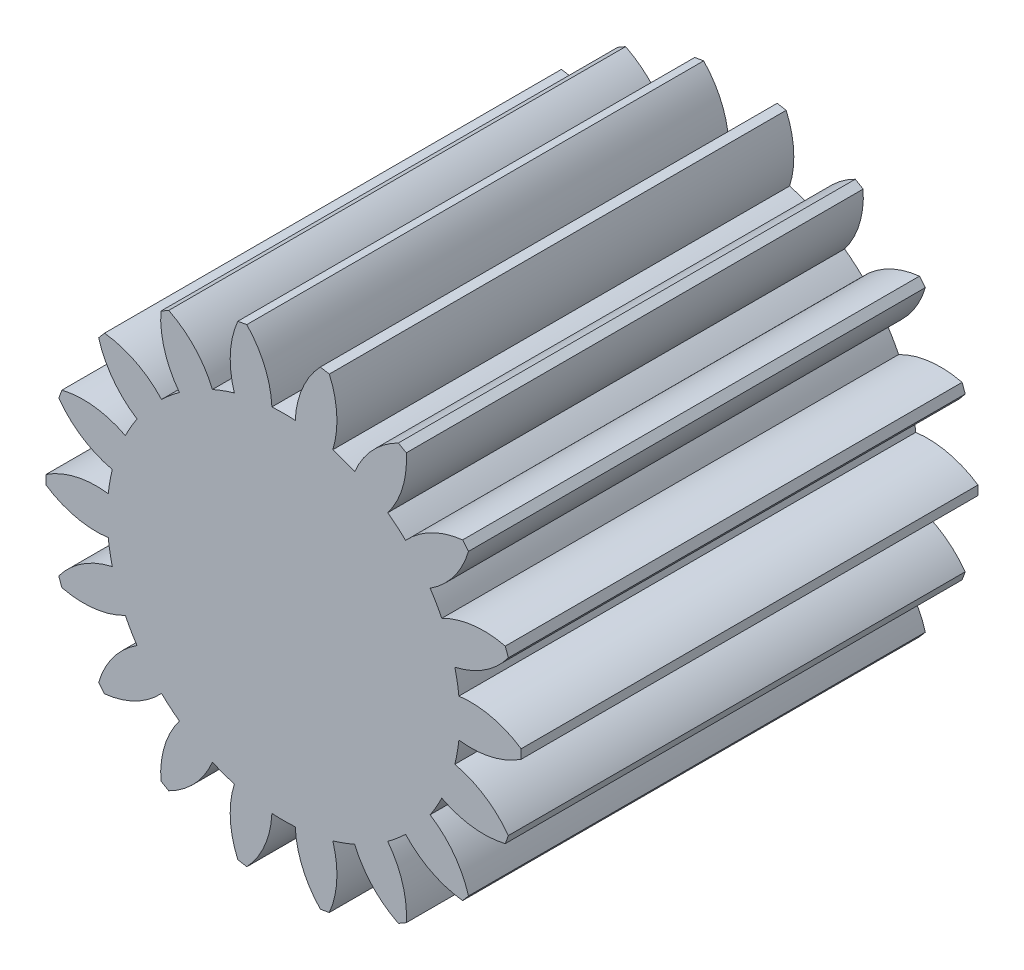
SolidWorks part; units mm, degrees
ref_plane "Front Plane" through (0, 0, 0) normal (0, 0, 1) x (1, 0, 0)
ref_plane "Top Plane" through (0, 0, 0) normal (0, 1, 0) x (1, 0, 0)
ref_plane "Right Plane" through (0, 0, 0) normal (1, 0, 0) x (0, 0, -1)
sketch "Sketch1" plane through (0, 0, 0) normal (0, 0, 1) x (1, 0, 0)
  arc A72 (4.0738, 2.7268) -> (4.9618, 3.9627) centre (2.7672, 4.6025) ccw
  arc A73 (4.9618, 3.9627) -> (4.7641, 4.1983) centre (0, 0) ccw
  arc A74 (4.7641, 4.1983) -> (3.3928, 3.5385) centre (5.0131, 1.9259) ccw
  arc A75 (3.3928, 3.5385) -> (2.8956, 3.9557) centre (0, 0) ccw
  arc A76 (2.8956, 3.9557) -> (3.3073, 5.4207) centre (1.0261, 5.2714) ccw
  arc A77 (3.3073, 5.4207) -> (3.0409, 5.5745) centre (0, 0) ccw
  arc A78 (3.0409, 5.5745) -> (1.9779, 4.4855) centre (4.0521, 3.5244) ccw
  arc A79 (1.9779, 4.4855) -> (1.368, 4.7075) centre (0, 0) ccw
  arc A80 (1.368, 4.7075) -> (1.2538, 6.225) centre (-0.8387, 5.3045) ccw
  arc A81 (1.2538, 6.225) -> (0.9509, 6.2784) centre (0, 0) ccw
  arc A82 (0.9509, 6.2784) -> (0.3245, 4.8914) centre (2.6023, 4.6977) ccw
  arc A83 (0.3245, 4.8914) -> (-0.3245, 4.8914) centre (0, 0) ccw
  arc A84 (-0.3245, 4.8914) -> (-0.9509, 6.2784) centre (-2.6023, 4.6977) ccw
  arc A85 (-0.9509, 6.2784) -> (-1.2538, 6.225) centre (0, 0) ccw
  arc A86 (-1.2538, 6.225) -> (-1.368, 4.7075) centre (0.8387, 5.3045) ccw
  arc A87 (-1.368, 4.7075) -> (-1.9779, 4.4855) centre (0, 0) ccw
  arc A88 (-1.9779, 4.4855) -> (-3.0409, 5.5745) centre (-4.0521, 3.5244) ccw
  arc A89 (-3.0409, 5.5745) -> (-3.3073, 5.4207) centre (0, 0) ccw
  arc A90 (-3.3073, 5.4207) -> (-2.8956, 3.9557) centre (-1.0261, 5.2714) ccw
  arc A91 (-2.8956, 3.9557) -> (-3.3928, 3.5385) centre (0, 0) ccw
  arc A92 (-3.3928, 3.5385) -> (-4.7641, 4.1983) centre (-5.0131, 1.9259) ccw
  arc A93 (-4.7641, 4.1983) -> (-4.9618, 3.9627) centre (0, 0) ccw
  arc A94 (-4.9618, 3.9627) -> (-4.0738, 2.7268) centre (-2.7672, 4.6025) ccw
  arc A95 (-4.0738, 2.7268) -> (-4.3984, 2.1647) centre (0, 0) ccw
  arc A96 (-4.3984, 2.1647) -> (-5.9127, 2.3157) centre (-5.3695, 0.0952) ccw
  arc A97 (-5.9127, 2.3157) -> (-6.0179, 2.0267) centre (0, 0) ccw
  arc A98 (-6.0179, 2.0267) -> (-4.7608, 1.169) centre (-4.1745, 3.3785) ccw
  arc A99 (-4.7608, 1.169) -> (-4.8735, 0.5298) centre (0, 0) ccw
  arc A100 (-4.8735, 0.5298) -> (-6.3481, 0.1538) centre (-5.0782, -1.747) ccw
  arc A101 (-6.3481, 0.1538) -> (-6.3481, -0.1538) centre (0, 0) ccw
  arc A102 (-6.3481, -0.1538) -> (-4.8735, -0.5298) centre (-5.0782, 1.747) ccw
  arc A103 (-4.8735, -0.5298) -> (-4.7608, -1.169) centre (0, 0) ccw
  arc A104 (-4.7608, -1.169) -> (-6.0179, -2.0267) centre (-4.1745, -3.3785) ccw
  arc A105 (-6.0179, -2.0267) -> (-5.9127, -2.3157) centre (0, 0) ccw
  arc A106 (-5.9127, -2.3157) -> (-4.3984, -2.1647) centre (-5.3695, -0.0952) ccw
  arc A107 (-4.3984, -2.1647) -> (-4.0738, -2.7268) centre (0, 0) ccw
  arc A108 (-4.0738, -2.7268) -> (-4.9618, -3.9627) centre (-2.7672, -4.6025) ccw
  arc A109 (-4.9618, -3.9627) -> (-4.7641, -4.1983) centre (0, 0) ccw
  arc A110 (-4.7641, -4.1983) -> (-3.3928, -3.5385) centre (-5.0131, -1.9259) ccw
  arc A111 (-3.3928, -3.5385) -> (-2.8956, -3.9557) centre (0, 0) ccw
  arc A112 (-2.8956, -3.9557) -> (-3.3073, -5.4207) centre (-1.0261, -5.2714) ccw
  arc A113 (-3.3073, -5.4207) -> (-3.0409, -5.5745) centre (0, 0) ccw
  arc A114 (-3.0409, -5.5745) -> (-1.9779, -4.4855) centre (-4.0521, -3.5244) ccw
  arc A115 (-1.9779, -4.4855) -> (-1.368, -4.7075) centre (0, 0) ccw
  arc A116 (-1.368, -4.7075) -> (-1.2538, -6.225) centre (0.8387, -5.3045) ccw
  arc A117 (-1.2538, -6.225) -> (-0.9509, -6.2784) centre (0, 0) ccw
  arc A118 (-0.9509, -6.2784) -> (-0.3245, -4.8914) centre (-2.6023, -4.6977) ccw
  arc A119 (-0.3245, -4.8914) -> (0.3245, -4.8914) centre (0, 0) ccw
  arc A120 (0.3245, -4.8914) -> (0.9509, -6.2784) centre (2.6023, -4.6977) ccw
  arc A121 (0.9509, -6.2784) -> (1.2538, -6.225) centre (0, 0) ccw
  arc A122 (1.2538, -6.225) -> (1.368, -4.7075) centre (-0.8387, -5.3045) ccw
  arc A123 (1.368, -4.7075) -> (1.9779, -4.4855) centre (0, 0) ccw
  arc A124 (1.9779, -4.4855) -> (3.0409, -5.5745) centre (4.0521, -3.5244) ccw
  arc A125 (3.0409, -5.5745) -> (3.3073, -5.4207) centre (0, 0) ccw
  arc A126 (3.3073, -5.4207) -> (2.8956, -3.9557) centre (1.0261, -5.2714) ccw
  arc A127 (2.8956, -3.9557) -> (3.3928, -3.5385) centre (0, 0) ccw
  arc A128 (3.3928, -3.5385) -> (4.7641, -4.1983) centre (5.0131, -1.9259) ccw
  arc A129 (4.7641, -4.1983) -> (4.9618, -3.9627) centre (0, 0) ccw
  arc A130 (4.9618, -3.9627) -> (4.0738, -2.7268) centre (2.7672, -4.6025) ccw
  arc A131 (4.0738, -2.7268) -> (4.3984, -2.1647) centre (0, 0) ccw
  arc A132 (4.3984, -2.1647) -> (5.9127, -2.3157) centre (5.3695, -0.0952) ccw
  arc A133 (5.9127, -2.3157) -> (6.0179, -2.0267) centre (0, 0) ccw
  arc A134 (6.0179, -2.0267) -> (4.7608, -1.169) centre (4.1745, -3.3785) ccw
  arc A135 (4.7608, -1.169) -> (4.8735, -0.5298) centre (0, 0) ccw
  arc A136 (4.8735, -0.5298) -> (6.3481, -0.1538) centre (5.0782, 1.747) ccw
  arc A137 (6.3481, -0.1538) -> (6.3481, 0.1538) centre (0, 0) ccw
  arc A138 (6.3481, 0.1538) -> (4.8735, 0.5298) centre (5.0782, -1.747) ccw
  arc A139 (4.8735, 0.5298) -> (4.7608, 1.169) centre (0, 0) ccw
  arc A140 (4.7608, 1.169) -> (6.0179, 2.0267) centre (4.1745, 3.3785) ccw
  arc A141 (6.0179, 2.0267) -> (5.9127, 2.3157) centre (0, 0) ccw
  arc A142 (5.9127, 2.3157) -> (4.3984, 2.1647) centre (5.3695, 0.0952) ccw
  arc A143 (4.3984, 2.1647) -> (4.0738, 2.7268) centre (0, 0) ccw
  arc A144 (4.0738, 2.7268) -> (4.9618, 3.9627) centre (2.7672, 4.6025) ccw
  arc A145 (4.9618, 3.9627) -> (4.7641, 4.1983) centre (0, 0) ccw
  arc A146 (4.7641, 4.1983) -> (3.3928, 3.5385) centre (5.0131, 1.9259) ccw
  arc A147 (3.3928, 3.5385) -> (2.8956, 3.9557) centre (0, 0) ccw
  arc A148 (2.8956, 3.9557) -> (3.3073, 5.4207) centre (1.0261, 5.2714) ccw
  arc A149 (3.3073, 5.4207) -> (3.0409, 5.5745) centre (0, 0) ccw
  arc A150 (3.0409, 5.5745) -> (1.9779, 4.4855) centre (4.0521, 3.5244) ccw
  arc A151 (1.9779, 4.4855) -> (1.368, 4.7075) centre (0, 0) ccw
  arc A152 (1.368, 4.7075) -> (1.2538, 6.225) centre (-0.8387, 5.3045) ccw
  arc A153 (1.2538, 6.225) -> (0.9509, 6.2784) centre (0, 0) ccw
  arc A154 (0.9509, 6.2784) -> (0.3245, 4.8914) centre (2.6023, 4.6977) ccw
  arc A155 (0.3245, 4.8914) -> (-0.3245, 4.8914) centre (0, 0) ccw
  arc A156 (-0.3245, 4.8914) -> (-0.9509, 6.2784) centre (-2.6023, 4.6977) ccw
  arc A157 (-0.9509, 6.2784) -> (-1.2538, 6.225) centre (0, 0) ccw
  arc A158 (-1.2538, 6.225) -> (-1.368, 4.7075) centre (0.8387, 5.3045) ccw
  arc A159 (-1.368, 4.7075) -> (-1.9779, 4.4855) centre (0, 0) ccw
  arc A160 (-1.9779, 4.4855) -> (-3.0409, 5.5745) centre (-4.0521, 3.5244) ccw
  arc A161 (-3.0409, 5.5745) -> (-3.3073, 5.4207) centre (0, 0) ccw
  arc A162 (-3.3073, 5.4207) -> (-2.8956, 3.9557) centre (-1.0261, 5.2714) ccw
  arc A163 (-2.8956, 3.9557) -> (-3.3928, 3.5385) centre (0, 0) ccw
  arc A164 (-3.3928, 3.5385) -> (-4.7641, 4.1983) centre (-5.0131, 1.9259) ccw
  arc A165 (-4.7641, 4.1983) -> (-4.9618, 3.9627) centre (0, 0) ccw
  arc A166 (-4.9618, 3.9627) -> (-4.0738, 2.7268) centre (-2.7672, 4.6025) ccw
  arc A167 (-4.0738, 2.7268) -> (-4.3984, 2.1647) centre (0, 0) ccw
  arc A168 (-4.3984, 2.1647) -> (-5.9127, 2.3157) centre (-5.3695, 0.0952) ccw
  arc A169 (-5.9127, 2.3157) -> (-6.0179, 2.0267) centre (0, 0) ccw
  arc A170 (-6.0179, 2.0267) -> (-4.7608, 1.169) centre (-4.1745, 3.3785) ccw
  arc A171 (-4.7608, 1.169) -> (-4.8735, 0.5298) centre (0, 0) ccw
  arc A172 (-4.8735, 0.5298) -> (-6.3481, 0.1538) centre (-5.0782, -1.747) ccw
  arc A173 (-6.3481, 0.1538) -> (-6.3481, -0.1538) centre (0, 0) ccw
  arc A174 (-6.3481, -0.1538) -> (-4.8735, -0.5298) centre (-5.0782, 1.747) ccw
  arc A175 (-4.8735, -0.5298) -> (-4.7608, -1.169) centre (0, 0) ccw
  arc A176 (-4.7608, -1.169) -> (-6.0179, -2.0267) centre (-4.1745, -3.3785) ccw
  arc A177 (-6.0179, -2.0267) -> (-5.9127, -2.3157) centre (0, 0) ccw
  arc A178 (-5.9127, -2.3157) -> (-4.3984, -2.1647) centre (-5.3695, -0.0952) ccw
  arc A179 (-4.3984, -2.1647) -> (-4.0738, -2.7268) centre (0, 0) ccw
  arc A180 (-4.0738, -2.7268) -> (-4.9618, -3.9627) centre (-2.7672, -4.6025) ccw
  arc A181 (-4.9618, -3.9627) -> (-4.7641, -4.1983) centre (0, 0) ccw
  arc A182 (-4.7641, -4.1983) -> (-3.3928, -3.5385) centre (-5.0131, -1.9259) ccw
  arc A183 (-3.3928, -3.5385) -> (-2.8956, -3.9557) centre (0, 0) ccw
  arc A184 (-2.8956, -3.9557) -> (-3.3073, -5.4207) centre (-1.0261, -5.2714) ccw
  arc A185 (-3.3073, -5.4207) -> (-3.0409, -5.5745) centre (0, 0) ccw
  arc A186 (-3.0409, -5.5745) -> (-1.9779, -4.4855) centre (-4.0521, -3.5244) ccw
  arc A187 (-1.9779, -4.4855) -> (-1.368, -4.7075) centre (0, 0) ccw
  arc A188 (-1.368, -4.7075) -> (-1.2538, -6.225) centre (0.8387, -5.3045) ccw
  arc A189 (-1.2538, -6.225) -> (-0.9509, -6.2784) centre (0, 0) ccw
  arc A190 (-0.9509, -6.2784) -> (-0.3245, -4.8914) centre (-2.6023, -4.6977) ccw
  arc A191 (-0.3245, -4.8914) -> (0.3245, -4.8914) centre (0, 0) ccw
  arc A192 (0.3245, -4.8914) -> (0.9509, -6.2784) centre (2.6023, -4.6977) ccw
  arc A193 (0.9509, -6.2784) -> (1.2538, -6.225) centre (0, 0) ccw
  arc A194 (1.2538, -6.225) -> (1.368, -4.7075) centre (-0.8387, -5.3045) ccw
  arc A195 (1.368, -4.7075) -> (1.9779, -4.4855) centre (0, 0) ccw
  arc A196 (1.9779, -4.4855) -> (3.0409, -5.5745) centre (4.0521, -3.5244) ccw
  arc A197 (3.0409, -5.5745) -> (3.3073, -5.4207) centre (0, 0) ccw
  arc A198 (3.3073, -5.4207) -> (2.8956, -3.9557) centre (1.0261, -5.2714) ccw
  arc A199 (2.8956, -3.9557) -> (3.3928, -3.5385) centre (0, 0) ccw
  arc A200 (3.3928, -3.5385) -> (4.7641, -4.1983) centre (5.0131, -1.9259) ccw
  arc A201 (4.7641, -4.1983) -> (4.9618, -3.9627) centre (0, 0) ccw
  arc A202 (4.9618, -3.9627) -> (4.0738, -2.7268) centre (2.7672, -4.6025) ccw
  arc A203 (4.0738, -2.7268) -> (4.3984, -2.1647) centre (0, 0) ccw
  arc A204 (4.3984, -2.1647) -> (5.9127, -2.3157) centre (5.3695, -0.0952) ccw
  arc A205 (5.9127, -2.3157) -> (6.0179, -2.0267) centre (0, 0) ccw
  arc A206 (6.0179, -2.0267) -> (4.7608, -1.169) centre (4.1745, -3.3785) ccw
  arc A207 (4.7608, -1.169) -> (4.8735, -0.5298) centre (0, 0) ccw
  arc A208 (4.8735, -0.5298) -> (6.3481, -0.1538) centre (5.0782, 1.747) ccw
  arc A209 (6.3481, -0.1538) -> (6.3481, 0.1538) centre (0, 0) ccw
  arc A210 (6.3481, 0.1538) -> (4.8735, 0.5298) centre (5.0782, -1.747) ccw
  arc A211 (4.8735, 0.5298) -> (4.7608, 1.169) centre (0, 0) ccw
  arc A212 (4.7608, 1.169) -> (6.0179, 2.0267) centre (4.1745, 3.3785) ccw
  arc A213 (6.0179, 2.0267) -> (5.9127, 2.3157) centre (0, 0) ccw
  arc A214 (5.9127, 2.3157) -> (4.3984, 2.1647) centre (5.3695, 0.0952) ccw
  arc A215 (4.3984, 2.1647) -> (4.0738, 2.7268) centre (0, 0) ccw
  dimension "D1" = 0
extrude "Boss-Extrude1" add sketch "Sketch1" against normal blind 12.7
sketch "Sketch3" plane through (0, 0, 0) normal (0, 0, 1) x (1, 0, 0)
  line L0 (6.604, 0.127) -> (6.604, -0.127)
  line L1 (6.2492, -2.1394) -> (6.1623, -2.378)
  line L2 (5.1406, -4.1477) -> (4.9773, -4.3423)
  line L3 (3.412, -5.6557) -> (3.192, -5.7827)
  line L4 (1.2718, -6.4816) -> (1.0217, -6.5257)
  line L5 (-1.0217, -6.5257) -> (-1.2718, -6.4816)
  line L6 (-3.192, -5.7827) -> (-3.412, -5.6557)
  line L7 (-4.9773, -4.3423) -> (-5.1406, -4.1477)
  line L8 (-6.1623, -2.378) -> (-6.2492, -2.1394)
  line L9 (-6.604, -0.127) -> (-6.604, 0.127)
  line L10 (-6.2492, 2.1394) -> (-6.1623, 2.378)
  line L11 (-5.1406, 4.1477) -> (-4.9773, 4.3423)
  line L12 (-3.412, 5.6557) -> (-3.192, 5.7827)
  line L13 (-1.2718, 6.4816) -> (-1.0217, 6.5257)
  line L14 (1.0217, 6.5257) -> (1.2718, 6.4816)
  line L15 (3.192, 5.7827) -> (3.412, 5.6557)
  line L16 (4.9773, 4.3423) -> (5.1406, 4.1477)
  line L17 (6.1623, 2.378) -> (6.2492, 2.1394)
  arc A0 (4.8735, -0.5298) -> (6.604, -0.127) centre (5.1993, 1.9892) ccw
  arc A1 (4.8735, 0.5298) -> (6.604, 0.127) centre (5.1993, -1.9892) cw
  arc A2 (4.8735, 0.5298) -> (4.7608, 1.169) centre (0, 0) ccw construction
  arc A3 (4.8735, 0.5298) -> (4.7608, 1.169) centre (0, 0) ccw
  arc A4 (4.7608, -1.169) -> (6.2492, -2.1394) centre (4.2054, -3.6475) cw
  arc A5 (4.3984, -2.1647) -> (6.1623, -2.378) centre (5.5661, 0.091) ccw
  arc A6 (4.7608, -1.169) -> (4.8735, -0.5298) centre (0, 0) ccw
  arc A7 (4.0738, -2.7268) -> (5.1406, -4.1477) centre (2.7042, -4.8659) cw
  arc A8 (3.3928, -3.5385) -> (4.9773, -4.3423) centre (5.2616, -1.8182) ccw
  arc A9 (4.0738, -2.7268) -> (4.3984, -2.1647) centre (0, 0) ccw
  arc A10 (2.8956, -3.9557) -> (3.412, -5.6557) centre (0.8769, -5.4973) cw
  arc A11 (1.9779, -4.4855) -> (3.192, -5.7827) centre (4.3224, -3.5081) ccw
  arc A12 (2.8956, -3.9557) -> (3.3928, -3.5385) centre (0, 0) ccw
  arc A13 (1.368, -4.7075) -> (1.2718, -6.4816) centre (-1.0562, -5.4657) cw
  arc A14 (0.3245, -4.8914) -> (1.0217, -6.5257) centre (2.8619, -4.7749) ccw
  arc A15 (1.368, -4.7075) -> (1.9779, -4.4855) centre (0, 0) ccw
  arc A16 (-0.3245, -4.8914) -> (-1.0217, -6.5257) centre (-2.8619, -4.7749) cw
  arc A17 (-1.368, -4.7075) -> (-1.2718, -6.4816) centre (1.0562, -5.4657) ccw
  arc A18 (-0.3245, -4.8914) -> (0.3245, -4.8914) centre (0, 0) ccw
  arc A19 (-1.9779, -4.4855) -> (-3.192, -5.7827) centre (-4.3224, -3.5081) cw
  arc A20 (-2.8956, -3.9557) -> (-3.412, -5.6557) centre (-0.8769, -5.4973) ccw
  arc A21 (-1.9779, -4.4855) -> (-1.368, -4.7075) centre (0, 0) ccw
  arc A22 (-3.3928, -3.5385) -> (-4.9773, -4.3423) centre (-5.2616, -1.8182) cw
  arc A23 (-4.0738, -2.7268) -> (-5.1406, -4.1477) centre (-2.7042, -4.8659) ccw
  arc A24 (-3.3928, -3.5385) -> (-2.8956, -3.9557) centre (0, 0) ccw
  arc A25 (-4.3984, -2.1647) -> (-6.1623, -2.378) centre (-5.5661, 0.091) cw
  arc A26 (-4.7608, -1.169) -> (-6.2492, -2.1394) centre (-4.2054, -3.6475) ccw
  arc A27 (-4.3984, -2.1647) -> (-4.0738, -2.7268) centre (0, 0) ccw
  arc A28 (-4.8735, -0.5298) -> (-6.604, -0.127) centre (-5.1993, 1.9892) cw
  arc A29 (-4.8735, 0.5298) -> (-6.604, 0.127) centre (-5.1993, -1.9892) ccw
  arc A30 (-4.8735, -0.5298) -> (-4.7608, -1.169) centre (0, 0) ccw
  arc A31 (-4.7608, 1.169) -> (-6.2492, 2.1394) centre (-4.2054, 3.6475) cw
  arc A32 (-4.3984, 2.1647) -> (-6.1623, 2.378) centre (-5.5661, -0.091) ccw
  arc A33 (-4.7608, 1.169) -> (-4.8735, 0.5298) centre (0, 0) ccw
  arc A34 (-4.0738, 2.7268) -> (-5.1406, 4.1477) centre (-2.7042, 4.8659) cw
  arc A35 (-3.3928, 3.5385) -> (-4.9773, 4.3423) centre (-5.2616, 1.8182) ccw
  arc A36 (-4.0738, 2.7268) -> (-4.3984, 2.1647) centre (0, 0) ccw
  arc A37 (-2.8956, 3.9557) -> (-3.412, 5.6557) centre (-0.8769, 5.4973) cw
  arc A38 (-1.9779, 4.4855) -> (-3.192, 5.7827) centre (-4.3224, 3.5081) ccw
  arc A39 (-2.8956, 3.9557) -> (-3.3928, 3.5385) centre (0, 0) ccw
  arc A40 (-1.368, 4.7075) -> (-1.2718, 6.4816) centre (1.0562, 5.4657) cw
  arc A41 (-0.3245, 4.8914) -> (-1.0217, 6.5257) centre (-2.8619, 4.7749) ccw
  arc A42 (-1.368, 4.7075) -> (-1.9779, 4.4855) centre (0, 0) ccw
  arc A43 (0.3245, 4.8914) -> (1.0217, 6.5257) centre (2.8619, 4.7749) cw
  arc A44 (1.368, 4.7075) -> (1.2718, 6.4816) centre (-1.0562, 5.4657) ccw
  arc A45 (0.3245, 4.8914) -> (-0.3245, 4.8914) centre (0, 0) ccw
  arc A46 (1.9779, 4.4855) -> (3.192, 5.7827) centre (4.3224, 3.5081) cw
  arc A47 (2.8956, 3.9557) -> (3.412, 5.6557) centre (0.8769, 5.4973) ccw
  arc A48 (1.9779, 4.4855) -> (1.368, 4.7075) centre (0, 0) ccw
  arc A49 (3.3928, 3.5385) -> (4.9773, 4.3423) centre (5.2616, 1.8182) cw
  arc A50 (4.0738, 2.7268) -> (5.1406, 4.1477) centre (2.7042, 4.8659) ccw
  arc A51 (3.3928, 3.5385) -> (2.8956, 3.9557) centre (0, 0) ccw
  arc A52 (4.3984, 2.1647) -> (6.1623, 2.378) centre (5.5661, -0.091) cw
  arc A53 (4.7608, 1.169) -> (6.2492, 2.1394) centre (4.2054, 3.6475) ccw
  arc A54 (4.3984, 2.1647) -> (4.0738, 2.7268) centre (0, 0) ccw
  point P4 (6.604, 0)
  point P133 (0, 0)
  dimension "D1" = 2.54
  dimension "D4" = 2.54
  dimension "D2" = 6.604
  dimension "D3" = 0.254
  dimension "D5" = 18
extrude "Larger_Teeth" add sketch "Sketch3" against normal up to surface (12.7 mm away) up to face at (0, 0, -12.7)
sketch "Sketch2" plane through (0, 0, 0) normal (0, 0, 1) x (1, 0, 0)
  circle A0 centre (0, 0) radius 4.699
  dimension "D1" = 9.398
extrude "Cut-Extrude1" cut sketch "Sketch2" against normal up to surface (10.16 mm away) from offset 2.54 up to face at (0, 0, -12.7)
